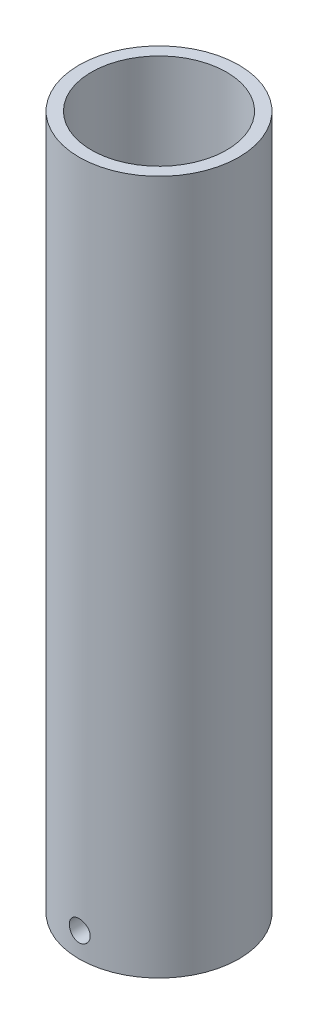
SolidWorks part; units mm, degrees
ref_plane "Front" through (0, 0, 0) normal (0, 0, 1) x (1, 0, 0)
ref_plane "Top" through (0, 0, 0) normal (0, 1, 0) x (1, 0, 0)
ref_plane "Right" through (0, 0, 0) normal (1, 0, 0) x (0, 0, -1)
sketch "Sketch1" plane through (0, 0, 0) normal (0, 0, 1) x (1, 0, 0)
  line L0 (0, 0) -> (0, 144.7737) construction
  line L1 (0, 0) -> (-0.2, 0) construction
  line L2 (-0.2, 0) -> (-0.2, 8)
  line L4 (-5, 22) -> (-5, 29)
  line L5 (-5, 29) -> (-11, 32.6052)
  line L6 (-11, 32.6052) -> (-11, 116)
  line L7 (-11, 116) -> (-13, 116)
  line L16 (-0.2, 0) -> (-13, 0)
  line L18 (-3.25, 20.9485) -> (-3.25, 11.9914)
  line L21 (-1.6, 11) -> (-1.6, 8.8412)
  line L23 (-1.6, 8.8412) -> (-0.2, 8)
  line L24 (-1.6, 11) -> (-3.25, 11.9914)
  line L25 (-13, 116) -> (-13, 0)
  line L26 (-5, 22) -> (-3.25, 20.9485)
  line L27 (-5, 29) -> (0, 25.9957) construction
  line L28 (-3.25, 20.9485) -> (0, 18.9957) construction
  line L29 (-1.6, 11) -> (0, 10.0386) construction
  line L30 (-0.2, 8) -> (0, 7.8798) construction
  dimension "D2" = 0.4
  dimension "D3" = 7
  dimension "D4" = 10
  dimension "D5" = 6.5
  dimension "D6" = 59
  dimension "D7" = 87
  dimension "D8" = 22
  dimension "D9" = 11
  dimension "D10" = 3.2
  dimension "D11" = 3
  dimension "D12" = 2
  dimension "D13" = 8
  dimension "D14" = 59
  dimension "D15" = 59
  dimension "D16" = 59
revolve "Revolve1" add sketch "Sketch1" angle 360 about L0
ref_plane "Plane2" through (0, 0, 13) normal (0, 0, 1) x (1, 0, 0)
sketch "Sketch7" plane through (0, 0, 0) normal (0, -1, 0) x (1, 0, 0)
  circle A0 centre (0, 0) radius 13
  circle A1 centre (0, 0) radius 8
  circle A2 centre (0, 0) radius 13 construction
  dimension "D1" = 5
extrude "Cut-Extrude3" cut sketch "Sketch7" against normal blind 3
sketch "Sketch6" plane through (0, 0, 13) normal (0, 0, 1) x (1, 0, 0)
  line L0 (0, 7) -> (0, 0) construction
  line L1 (-13, 3) -> (13, 3) construction
  circle A0 centre (0, 7) radius 1.7
  dimension "D2" = 3.4
  dimension "D1" = 4
extrude "Cut-Extrude2" cut sketch "Sketch6" against normal blind 8
